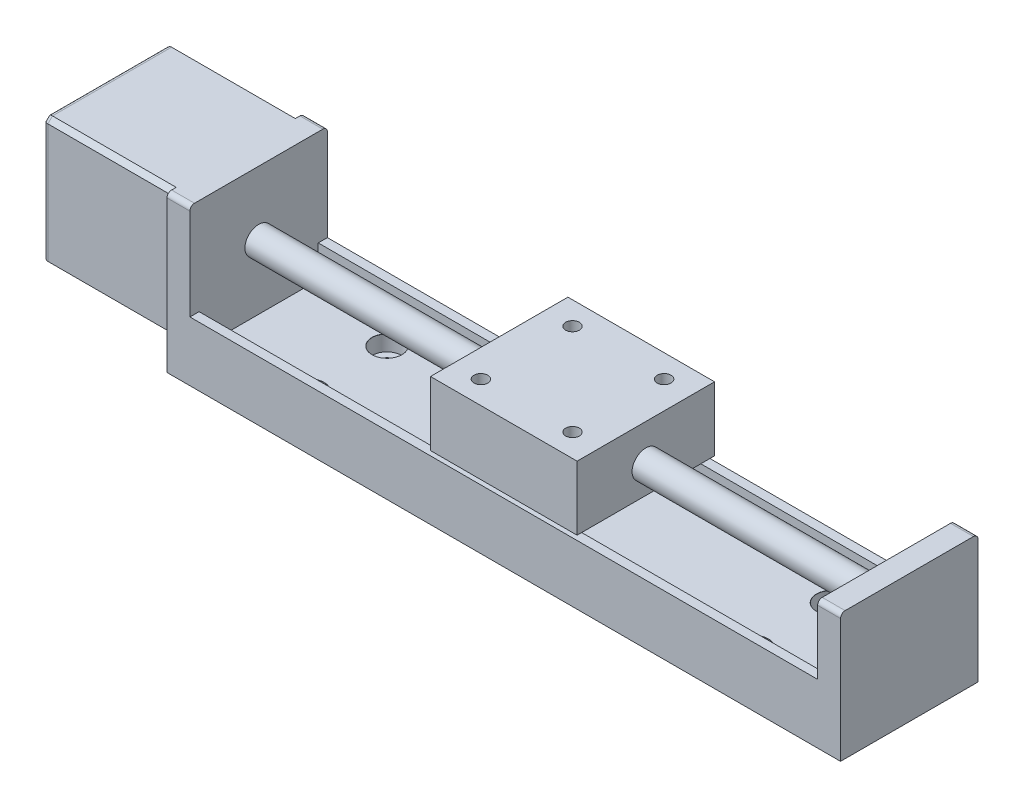
SolidWorks part; units mm, degrees
material "1060 Alloy"
ref_plane "Front Plane" through (0, 0, 0) normal (0, 0, 1) x (1, 0, 0)
ref_plane "Top Plane" through (0, 0, 0) normal (0, 1, 0) x (1, 0, 0)
ref_plane "Right Plane" through (0, 0, 0) normal (1, 0, 0) x (0, 0, -1)
sketch "Sketch1" plane through (0, 0, 0) normal (0, 0, 1) x (1, 0, 0)
  line L0 (-103.5, 34) -> (-103.5, 6)
  line L1 (-103.5, 6) -> (-73.5, 6)
  line L2 (-73.5, 6) -> (-73.5, 0)
  line L3 (-73.5, 0) -> (73.5, 0)
  line L4 (73.5, 0) -> (73.5, 28)
  line L5 (73.5, 28) -> (68.5, 28)
  line L6 (68.5, 28) -> (68.5, 13)
  line L7 (68.5, 13) -> (-68.5, 13)
  line L8 (-68.5, 13) -> (-68.5, 34)
  line L11 (-68.5, 34) -> (-103.5, 34)
  point P11 (0, 0)
  dimension "D1" = 5
  dimension "D2" = 5
  dimension "D3" = 13
  dimension "D4" = 28
  dimension "D5" = 30
  dimension "D6" = 28
  dimension "D7" = 34
  dimension "D8" = 177
extrude "Boss-Extrude1" add sketch "Sketch1" along normal mid plane 30
sketch "Sketch2" plane through (0, 13, 0) normal (0, 1, 0) x (1, 0, 0)
  line L0 (-68.5, -15) -> (-68.5, 15) construction
  line L1 (-68.5, -13) -> (68.5, -13)
  line L2 (-68.5, -13) -> (-68.5, 13)
  line L3 (-68.5, 13) -> (68.5, 13)
  line L4 (68.5, -13) -> (68.5, 13)
  line L5 (-68.5, -13) -> (68.5, 13) construction
  line L6 (-68.5, 13) -> (68.5, -13) construction
  line L7 (68.5, -15) -> (-68.5, -15) construction
  point P0 (0, 0)
  dimension "D1" = 2
extrude "Cut-Extrude1" cut sketch "Sketch2" against normal offset from surface (7 mm away) 6 up to face at (0, 0, 0)
sketch "Sketch3" plane through (73.5, 0, 0) normal (1, 0, 0) x (0, 0, -1)
  circle A0 centre (0, 20) radius 3
  dimension "D1" = 20
  dimension "D2" = 6
extrude "Boss-Extrude2" add sketch "Sketch3" against normal up to surface (142 mm away) up to face at (-68.5, 16.5, 0)
sketch "Sketch4" plane through (0, 34, 0) normal (0, 1, 0) x (1, 0, 0)
  line L0 (-73.5, 14) -> (-73.5, -14) construction
  line L3 (-73.5, -14) -> (-101.5, -14)
  line L4 (-101.5, -14) -> (-101.5, 14)
  line L5 (-101.5, 14) -> (-73.5, 14)
  line L6 (-68.5, -13) -> (-68.5, 13) construction
  line L7 (-68.5, 0) -> (-73.5, 0) construction
  line L8 (-68.5, -15) -> (-68.5, 15) construction
  line L9 (-73.5, -14) -> (-73.5, -15)
  line L10 (-68.5, -15) -> (-103.5, -15) construction
  line L11 (-73.5, -15) -> (-103.5, -15)
  line L12 (-103.5, -15) -> (-103.5, 15)
  line L13 (-103.5, 15) -> (-73.5, 15)
  line L14 (-68.5, 15) -> (-103.5, 15) construction
  line L15 (-73.5, 15) -> (-73.5, 14)
  line M7 (-68.5, 15) -> (-103.5, 15)
  line M8 (-103.5, 15) -> (-103.5, -15)
  line M9 (-103.5, -15) -> (-68.5, -15)
  dimension "D1" = 5
  dimension "D2" = 28
  dimension "D3" = 28
extrude "Cut-Extrude2" cut sketch "Sketch4" against normal through all contours L15 L9 L3 L4 L5 M7 M8 M9
chamfer "Chamfer1" distance 1 angle 45 4 edges at (-87.5, 6, 14) (-87.5, 6, -14) (-87.5, 34, -14) (-87.5, 34, 14)
fillet "Fillet1" radius 1 8 edges at (-101.5, 6.5, -13.5) (-101.5, 20, -14) (-101.5, 33.5, -13.5) (-101.5, 34, 0) (-101.5, 33.5, 13.5) (-101.5, 20, 14) (-101.5, 6.5, 13.5) (-101.5, 6, 0)
fillet "Fillet2" radius 1 4 edges at (71, 28, 15) (71, 28, -15) (-71, 34, -15) (-71, 34, 15)
hole_wizard "CBORE for M3 Hex Socket Head Cap Screw1" positions "Sketch5" profile "Sketch6" counterbore size "M3" standard "ISO" end condition through all
sketch "Sketch5" plane through (0, 6, 0) normal (0, 1, 0) x (1, 0, 0)
  line L0 (-48.5, 8.0068) -> (48.5, 8.0068) construction
  line L1 (48.5, 8.0068) -> (48.5, -8.9932) construction
  line L2 (48.5, -8.9932) -> (-48.5, -8.9932) construction
  line L3 (-48.5, -8.9932) -> (-48.5, 8.0068) construction
  line L5 (68.5, -14) -> (68.5, 14) construction
  line L6 (-68.5, -13) -> (-68.5, 13) construction
  point P0 (-48.5, 8.0068)
  point P2 (-48.5, -8.9932)
  point P4 (48.5, 8.0068)
  point P6 (48.5, -8.9932)
  dimension "D1" = 17
  dimension "D2" = 20
  dimension "D3" = 20
sketch "Sketch6" plane through (-48.5, 6, -8.0068) normal (1, 0, 0) x (0, 0, 1)
  line L0 (0, 0) -> (0, 6)
  line L1 (0, 6) -> (1.7, 6)
  line L3 (1.7, 6) -> (1.7, 3.4)
  line L4 (3.25, 3.4) -> (1.7, 3.4)
  line L5 (3.25, 3.4) -> (3.25, 0.025)
  line L6 (3.25, 0.025) -> (3.275, 0)
  line L7 (3.275, 0) -> (0, 0)
  line L8 (-3.25, 0.025) -> (-3.275, 0) construction
  line L11 (0, -6.35) -> (0, 107.95) construction
  dimension "Thru Hole Dia." = 3.4
  dimension "Thru Hole Depth" = 6
  dimension "C'Bore Dia." = 6.5
  dimension "C'Bore Depth" = 3.4
  dimension "Near C'Sink Dia." = 6.55
  dimension "Near C'Sink Angle" = 90
sketch "Sketch7" plane through (0, 28, 0) normal (0, 1, 0) x (1, 0, 0)
  line L1 (-16, -15) -> (16, -15)
  line L2 (-16, -15) -> (-16, 15)
  line L3 (-16, 15) -> (16, 15)
  line L4 (16, -15) -> (16, 15)
  line L5 (-16, -15) -> (16, 15) construction
  line L6 (-16, 15) -> (16, -15) construction
  point P0 (0, 0)
  dimension "D1" = 30
  dimension "D2" = 32
extrude "Boss-Extrude3" add sketch "Sketch7" against normal offset from surface (14 mm away) 1 up to face at (0, 13, 14)
sketch "Sketch8" plane through (0, 28, 0) normal (0, 1, 0) x (1, 0, 0)
  line L0 (-10, 10) -> (10, 10) construction
  line L1 (10, 10) -> (10, -10) construction
  line L2 (10, -10) -> (-10, -10) construction
  line L3 (-10, -10) -> (-10, 10) construction
  line L4 (16, 15) -> (-16, 15) construction
  line L5 (-16, 15) -> (-16, -15) construction
  circle A0 centre (-10, 10) radius 1.5 construction
  circle A1 centre (10, 10) radius 1.5 construction
  circle A2 centre (10, -10) radius 1.5 construction
  circle A3 centre (-10, -10) radius 1.5 construction
  dimension "D1" = 3
  dimension "D2" = 17
  dimension "D3" = 17
  dimension "D4" = 3.5
  dimension "D5" = 4.5
hole_wizard "Hole1" positions "Sketch9" profile "Sketch10" legacy
sketch "Sketch9" plane through (0, 28, 0) normal (0, 1, 0) x (1, 0, 0)
  point P0 (10, 10)
  point P3 (10, -10)
  point P6 (-10, -10)
  point P9 (-10, 10)
sketch "Sketch10" plane through (10, 28, -10) normal (1, 0, 0) x (0, 0, 1)
  line L0 (0, 0) -> (0, 6)
  line L1 (0, 6) -> (1.5, 6)
  line L2 (1.5, 6) -> (1.5, 0)
  line L3 (1.5, 0) -> (0, 0)
  line L4 (0, 110) -> (0, -10) construction
  dimension "Diameter" = 3
  dimension "Depth" = 6
